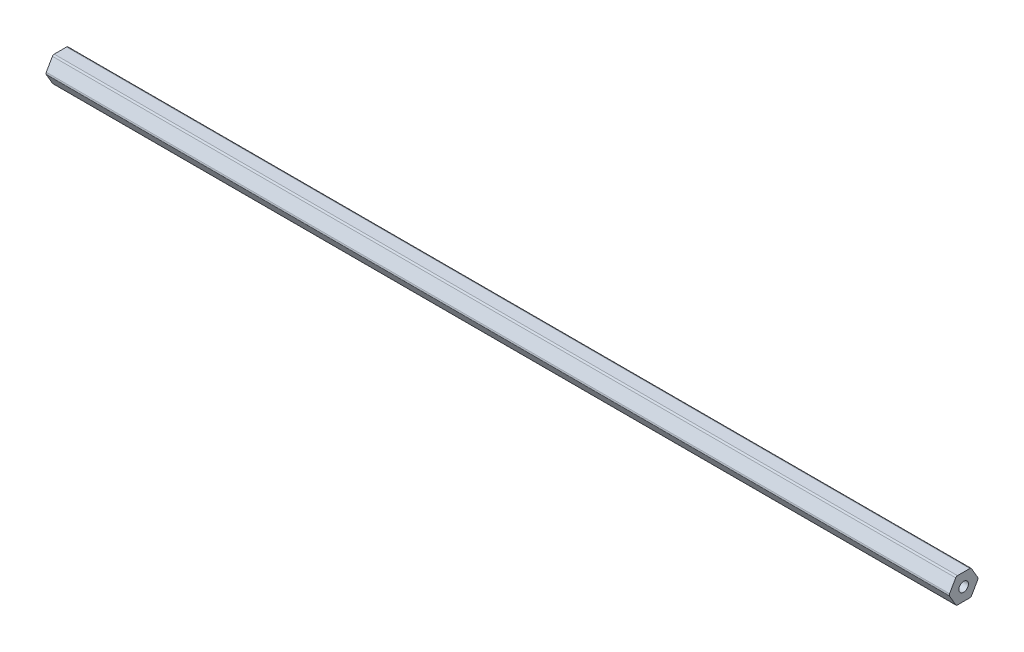
SolidWorks part; units mm, degrees
material "7075-T6 (SN)"
ref_plane "Front Plane" through (0, 0, 0) normal (0, 0, 1) x (1, 0, 0)
ref_plane "Top Plane" through (0, 0, 0) normal (0, 1, 0) x (1, 0, 0)
ref_plane "Right Plane" through (0, 0, 0) normal (1, 0, 0) x (0, 0, -1)
sketch "Sketch1" plane through (0, 0, 0) normal (1, 0, 0) x (0, 0, -1)
  line L1 (7.0391, 0.508) -> (3.9595, 5.842)
  line L2 (3.0796, 6.35) -> (-3.0796, 6.35)
  line L3 (-3.9595, 5.842) -> (-7.0391, 0.508)
  line L4 (-7.0391, -0.508) -> (-3.9595, -5.842)
  line L5 (-3.0796, -6.35) -> (3.0796, -6.35)
  line L6 (3.9595, -5.842) -> (7.0391, -0.508)
  circle A0 centre (0, 0) radius 6.35 construction
  arc A1 (3.0796, 6.35) -> (3.9595, 5.842) centre (3.0796, 5.334) cw
  arc A2 (7.0391, 0.508) -> (7.0391, -0.508) centre (6.1592, 0) cw
  arc A3 (3.9595, -5.842) -> (3.0796, -6.35) centre (3.0796, -5.334) cw
  arc A4 (-3.0796, -6.35) -> (-3.9595, -5.842) centre (-3.0796, -5.334) cw
  arc A5 (-7.0391, -0.508) -> (-7.0391, 0.508) centre (-6.1592, 0) cw
  arc A6 (-3.9595, 5.842) -> (-3.0796, 6.35) centre (-3.0796, 5.334) cw
  circle A7 centre (0, 0) radius 2.3813
  point P11 (3.6662, 6.35)
  point P14 (7.3323, 0)
  dimension "D1" = 12.7
  dimension "D3" = 1.016
  dimension "D4" = 4.7625
  dimension "D2" = 6.35
extrude "Boss-Extrude1" add sketch "Sketch1" along normal blind 225.425 and the other way blind 225.425
